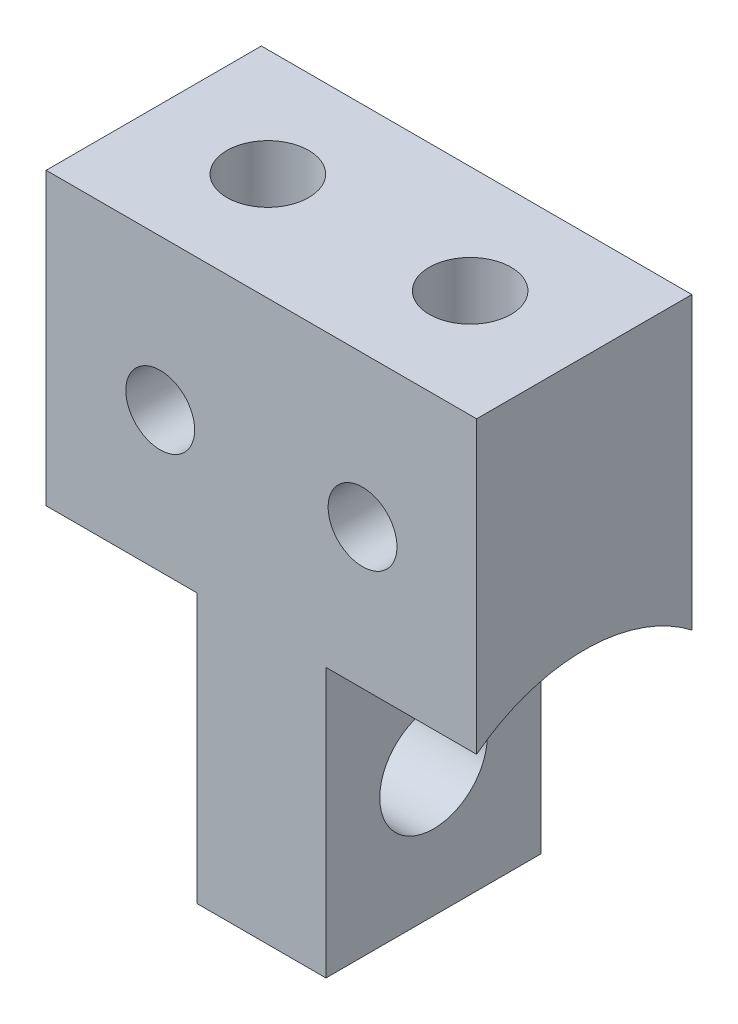
SolidWorks part; units mm, degrees
ref_plane "Front" through (0, 0, 0) normal (0, 0, 1) x (1, 0, 0)
ref_plane "Top" through (0, 0, 0) normal (0, 1, 0) x (1, 0, 0)
ref_plane "Right" through (0, 0, 0) normal (1, 0, 0) x (0, 0, -1)
sketch "Sketch1" plane through (0, 0, 0) normal (0, 0, 1) x (1, 0, 0)
  line L0 (0, 6.5) -> (0, -6.5) construction
  line L1 (-5, -6.5) -> (5, -6.5)
  line L2 (-5, -6.5) -> (-5, 6.5)
  line L3 (-5, 6.5) -> (5, 6.5)
  line L4 (5, -6.5) -> (5, 6.5)
  line L5 (-5, -6.5) -> (5, 6.5) construction
  line L6 (-5, 6.5) -> (5, -6.5) construction
  circle A0 centre (-2.35, 3) radius 0.8
  circle A1 centre (2.35, 3) radius 0.8
  point P0 (0, 0)
  dimension "D3" = 1.6
  dimension "D1" = 10
  dimension "D2" = 13
  dimension "D4" = 4.7
  dimension "D5" = 3.5
extrude "Boss-Extrude1" add sketch "Sketch1" along normal blind 5
sketch "Sketch3" plane through (-5, 0, 0) normal (-1, 0, 0) x (0, 0, 1)
  line L0 (2.5, -6.5) -> (2.5, -3.5) construction
  line L1 (5, -6.5) -> (0, -6.5) construction
  line L2 (-1.6, -3.5) -> (-1.6, -7.6)
  line L3 (-1.6, -7.6) -> (6.6, -7.6)
  line L4 (6.6, -7.6) -> (6.6, -3.5)
  arc A0 (6.6, -3.5) -> (-1.6, -3.5) centre (2.5, -3.5) ccw
  dimension "D2" = 8.2
  dimension "D1" = 3
extrude "Cut-Extrude2" cut sketch "Sketch3" against normal offset from surface (3.5 mm away) 1.5 up to plane "Right"
mirror "Mirror1" about plane through (0, 0, 0) normal (1, 0, 0) of "Cut-Extrude2"
sketch "Sketch4" plane through (-1.5, 0, 0) normal (-1, 0, 0) x (0, 0, 1)
  circle A0 centre (2.5, -3.5) radius 1.25
  dimension "D1" = 2.5
extrude "Cut-Extrude3" cut sketch "Sketch4" against normal through all
sketch "Sketch5" plane through (0, 6.5, 0) normal (0, 1, 0) x (1, 0, 0)
  line L0 (0, 0) -> (0, -5) construction
  line L1 (5, -5) -> (-5, -5) construction
  line L2 (0, -2.5) -> (-2.35, -2.5) construction
  circle A0 centre (-2.35, -2.5) radius 0.95
  circle A1 centre (2.35, -2.5) radius 0.95
  dimension "D2" = 1.9
  dimension "D1" = 4.7
extrude "Cut-Extrude4" cut sketch "Sketch5" against normal blind 3
